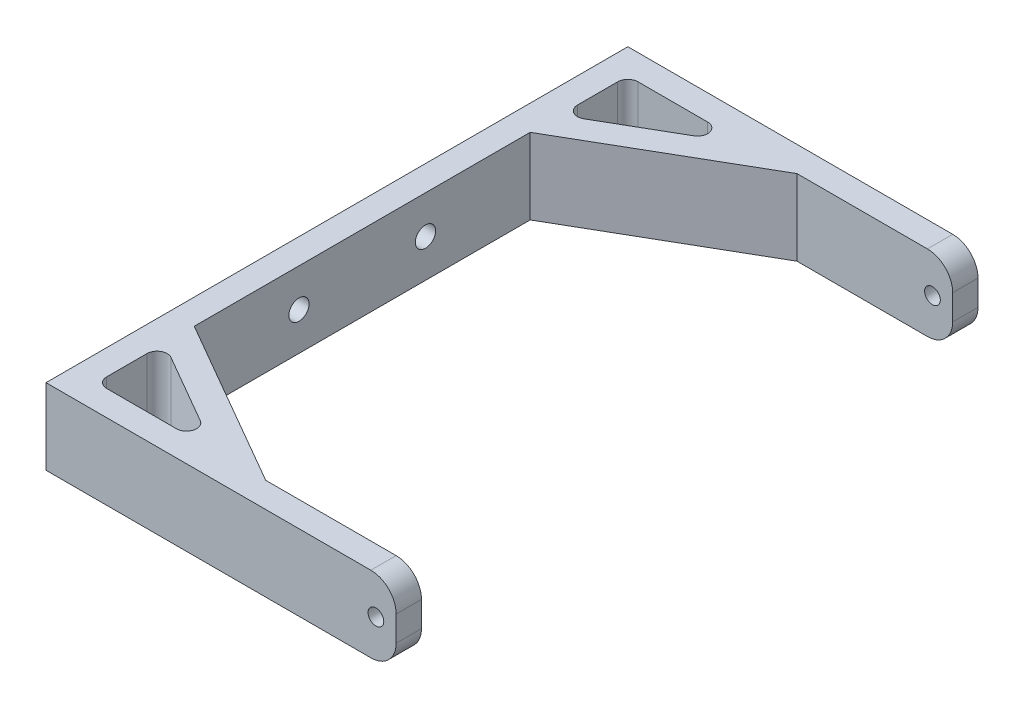
SolidWorks part; units mm, degrees
ref_plane "Front Plane" through (0, 0, 0) normal (0, 0, 1) x (1, 0, 0)
ref_plane "Top Plane" through (0, 0, 0) normal (0, 1, 0) x (1, 0, 0)
ref_plane "Right Plane" through (0, 0, 0) normal (1, 0, 0) x (0, 0, -1)
sketch "Sketch1" plane through (0, 0, 0) normal (0, 1, 0) x (1, 0, 0)
  line L0 (61.7079, 52.5) -> (66.7079, 52.5)
  line L2 (-2.5, -33.1989) -> (-2.5, 33.1989)
  line L4 (2.5, -33.1989) -> (2.5, 33.1989)
  line L5 (-2.5, -33.1989) -> (2.5, 33.1989) construction
  line L6 (-2.5, 33.1989) -> (2.5, -33.1989) construction
  line L7 (0, 0) -> (61.7079, 0) construction
  line L8 (66.7079, 52.5) -> (66.7079, 57.5)
  line L9 (66.7079, 57.5) -> (62.2412, 57.5)
  line L10 (61.7079, 52.5) -> (35.9304, 52.5)
  line L11 (35.9304, 52.5) -> (2.5, 33.1989)
  line L12 (-2.5, 33.1989) -> (-2.5, 36.1989)
  line L13 (2.5, 39.0857) -> (25.7343, 52.5)
  line L14 (62.2412, 57.5) -> (34.9278, 57.5)
  line L23 (34.9278, 57.5) -> (-2.5, 57.5)
  line L24 (-2.5, 57.5) -> (-2.5, 36.1989)
  line L25 (25.7343, 52.5) -> (2.5, 52.5)
  line L26 (2.5, 52.5) -> (2.5, 39.0857)
  line L27 (2.5, -52.5) -> (2.5, -39.0857)
  line L28 (25.7343, -52.5) -> (2.5, -52.5)
  line L29 (-2.5, -57.5) -> (-2.5, -36.1989)
  line L30 (34.9278, -57.5) -> (-2.5, -57.5)
  line L31 (62.2412, -57.5) -> (34.9278, -57.5)
  line L32 (2.5, -39.0857) -> (25.7343, -52.5)
  line L33 (-2.5, -33.1989) -> (-2.5, -36.1989)
  line L34 (35.9304, -52.5) -> (2.5, -33.1989)
  line L35 (61.7079, -52.5) -> (35.9304, -52.5)
  line L36 (66.7079, -57.5) -> (62.2412, -57.5)
  line L37 (66.7079, -52.5) -> (66.7079, -57.5)
  line L38 (61.7079, -52.5) -> (66.7079, -52.5)
  circle A0 centre (61.7079, 0) radius 52.5 construction
  point P0 (0, 0)
  dimension "D2" = 105
  dimension "D1" = 5
  dimension "D3" = 5
  dimension "D4" = 30
  dimension "D5" = 3
  dimension "D6" = 5
extrude "Boss-Extrude1" add sketch "Sketch1" along normal blind 15
sketch "Sketch2" plane through (0, 0, 57.5) normal (0, 0, 1) x (1, 0, 0)
  line L0 (62.7079, 15) -> (62.7079, 0) construction
  line L1 (-2.5, 15) -> (66.7079, 15) construction
  line L2 (-2.5, 0) -> (66.7079, 0) construction
  line L3 (66.7079, 15) -> (66.7079, 0) construction
  circle A0 centre (62.7079, 7.5) radius 1.55
  dimension "D1" = 3.1
  dimension "D2" = 4
extrude "Cut-Extrude1" cut sketch "Sketch2" against normal through all and the other way through all
fillet "Fillet1" radius 2 6 edges at (2.5, 7.5, -39.0857) (25.7343, 7.5, -52.5) (2.5, 7.5, -52.5) (25.7343, 7.5, 52.5) (2.5, 7.5, 52.5) (2.5, 7.5, 39.0857)
fillet "Fillet2" radius 5 4 edges at (66.7079, 0, 55) (66.7079, 15, 55) (66.7079, 0, -55) (66.7079, 15, -55)
sketch "Sketch3" plane through (2.5, 0, 0) normal (1, 0, 0) x (0, 0, -1)
  line L0 (0, 0) -> (0, 15) construction
  line L1 (-33.1989, 0) -> (33.1989, 0) construction
  line L2 (-33.1989, 15) -> (33.1989, 15) construction
  line L3 (-12.5, 7.5) -> (12.5, 7.5) construction
  circle A0 centre (-12.5, 7.5) radius 2
  circle A1 centre (12.5, 7.5) radius 2
  point P9 (0, 7.5)
  dimension "D1" = 4
  dimension "D2" = 25
extrude "Cut-Extrude2" cut sketch "Sketch3" against normal through all
